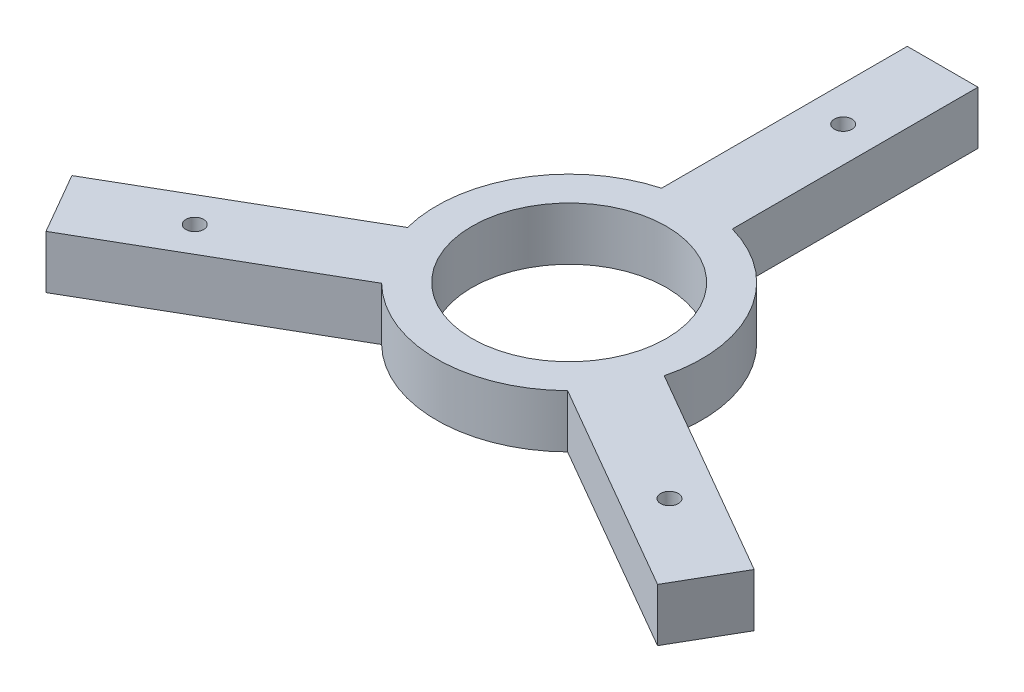
SolidWorks part; units mm, degrees
ref_plane "Alzado" through (0, 0, 0) normal (0, 0, 1) x (1, 0, 0)
ref_plane "Planta" through (0, 0, 0) normal (0, 1, 0) x (1, 0, 0)
ref_plane "Vista lateral" through (0, 0, 0) normal (1, 0, 0) x (0, 0, -1)
sketch "Croquis1" plane through (0, 0, 0) normal (0, 1, 0) x (1, 0, 0)
  line L0 (0, 0) -> (0, 33.9991) construction
  line L1 (0, 0) -> (29.4441, -16.9996) construction
  line L2 (0, 0) -> (-29.4441, -16.9996) construction
  line L4 (-19.2935, -8.8297) -> (-17.2935, -12.2938)
  line L5 (-17.2935, -12.2938) -> (-5.26, -5.3463)
  line L6 (-7.26, -1.8822) -> (-19.2935, -8.8297)
  line L7 (-3.4966, -4.3282) -> (-3.4371, -4.2938)
  line L8 (-2, 21.1235) -> (-2, 7.2284)
  line L9 (2, 21.1235) -> (-2, 21.1235)
  line L10 (2, 7.2284) -> (2, 21.1235)
  line L11 (19.2935, -8.8297) -> (7.26, -1.8822)
  line L12 (17.2935, -12.2938) -> (19.2935, -8.8297)
  line L13 (5.26, -5.3463) -> (17.2935, -12.2938)
  circle A0 centre (0, 0) radius 26 construction
  circle A1 centre (0, 0) radius 5 construction
  circle A2 centre (0, 15.5) radius 10.5 construction
  circle A3 centre (-13.4234, -7.75) radius 10.5 construction
  circle A4 centre (13.4234, -7.75) radius 10.5 construction
  circle A5 centre (0, 0) radius 5.5
  circle A6 centre (-13.4234, -7.75) radius 0.5
  arc A7 (-5.26, -5.3463) -> (5.26, -5.3463) centre (0, 0) ccw
  arc A8 (-2, 7.2284) -> (-7.26, -1.8822) centre (0, 0) ccw
  arc A9 (7.26, -1.8822) -> (2, 7.2284) centre (0, 0) ccw
  circle A10 centre (0, 15.5) radius 0.5
  circle A11 centre (13.4234, -7.75) radius 0.5
  point P34 (0, 0)
  point P39 (0, 0)
  dimension "D1" = 52
  dimension "D4" = 10
  dimension "D5" = 21
  dimension "D6" = 11
  dimension "D8" = 1
  dimension "D3" = 15
  dimension "D2" = 120
  dimension "D9" = 4
  dimension "D10" = 120
  dimension "D11" = 3
  dimension "D12" = 3
extrude "Saliente-Extruir2" add sketch "Croquis1" along normal blind 3 contours A5 | A6 | L6 L4 L5 A7 L13 L12 L11 A9 L10 L9 L8 A8 | A11 | A10
